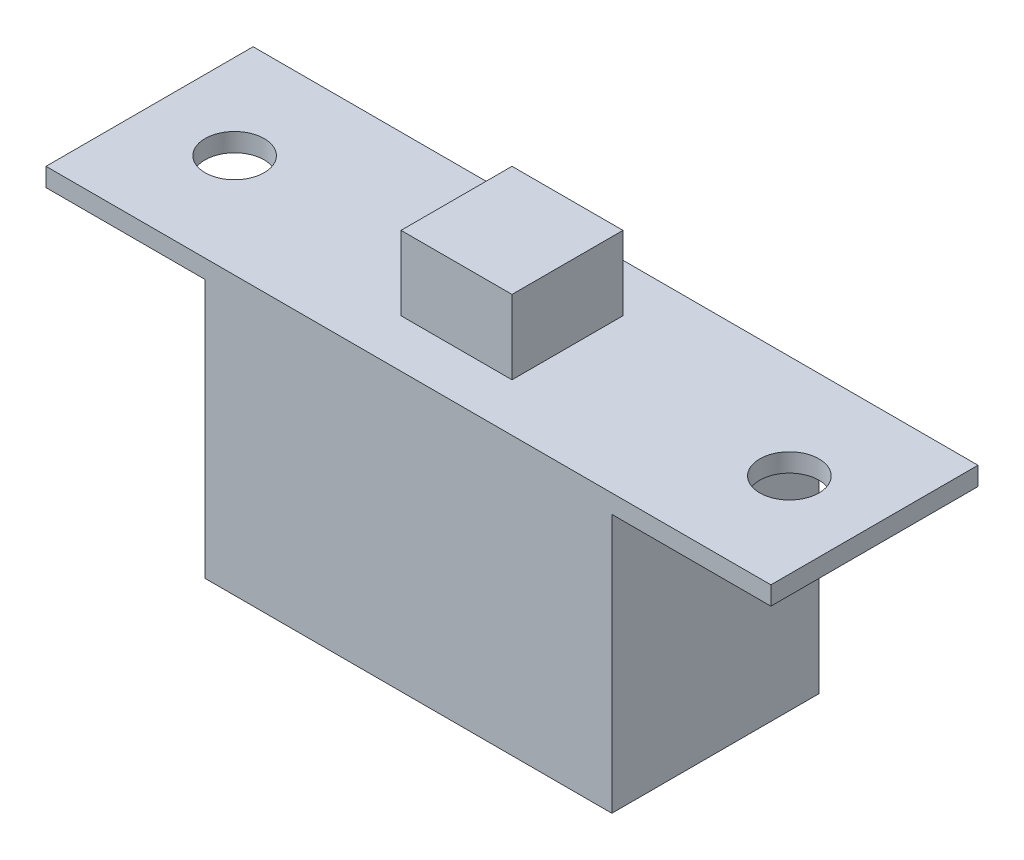
SolidWorks part; units mm, degrees
material "Unlegierter Baustahl"
ref_plane "Ebene vorne" through (0, 0, 0) normal (0, 0, 1) x (1, 0, 0)
ref_plane "Ebene oben" through (0, 0, 0) normal (0, 1, 0) x (1, 0, 0)
ref_plane "Ebene rechts" through (0, 0, 0) normal (1, 0, 0) x (0, 0, -1)
sketch "Skizze1" plane through (0, 0, 0) normal (0, 0, 1) x (1, 0, 0)
  line L0 (-9.8, -2) -> (-1.5, -2)
  line L1 (-1.5, -2) -> (-1.5, 0)
  line L2 (-1.5, 0) -> (1.5, 0)
  line L3 (0, 0) -> (0, -9.5) construction
  line L4 (-9.8, -2) -> (-9.8, -2.5)
  line L5 (-9.8, -2.5) -> (-5.5, -2.5)
  line L6 (-5.5, -2.5) -> (-5.5, -9.5)
  line L7 (-5.5, -9.5) -> (5.5, -9.5)
  line L8 (5.5, -2.5) -> (5.5, -9.5)
  line L9 (9.8, -2.5) -> (5.5, -2.5)
  line L10 (9.8, -2) -> (9.8, -2.5)
  line L11 (1.5, -2) -> (1.5, 0)
  line L12 (9.8, -2) -> (1.5, -2)
  dimension "D1" = 3
  dimension "D2" = 19.6
  dimension "D3" = 11
  dimension "D4" = 0.5
  dimension "D5" = 2
  dimension "D6" = 7
extrude "Aufsatz-Linear austragen1" add sketch "Skizze1" along normal mid plane 5.6
sketch "Skizze2" plane through (0, 0, 0) normal (0, 0, 1) x (1, 0, 0)
  line L1 (1.5, -2) -> (-1.5, -2)
  line L2 (1.5, -2) -> (1.5, 0)
  line L3 (1.5, 0) -> (-1.5, 0)
  line L4 (-1.5, -2) -> (-1.5, 0)
  line L5 (1.5, -2) -> (-1.5, 0) construction
  line L6 (1.5, 0) -> (-1.5, -2) construction
  point P0 (0, -1)
extrude "Schnitt-Linear austragen1" cut sketch "Skizze2" along normal through all from offset 1.5
mirror "Spiegeln1" about plane through (0, 0, 0) normal (0, 0, 1) of "Schnitt-Linear austragen1"
hole_wizard "M2 Gewindebohrung1" positions "Skizze3" profile "Skizze4" tap size "M2" standard "DIN" end condition through all
sketch "Skizze3" plane through (0, -2, 0) normal (0, 1, 0) x (1, 0, 0)
  point P0 (-7.5, 0)
  point P2 (7.5, 0)
  dimension "D1" = 7.5
  dimension "D2" = 7.5
sketch "Skizze4" plane through (-7.5, -2, 0) normal (1, 0, 0) x (0, 0, 1)
  line L0 (0, 0) -> (0, 7.5)
  line L1 (0, 7.5) -> (0.8, 7.5)
  line L2 (0.8, 7.5) -> (0.8, 0)
  line L5 (0.8, 0) -> (0, 0)
  line L11 (0, -6.35) -> (0, 107.95) construction
  dimension "Bohrerdurchmesser" = 1.6
  dimension "Bohrungstiefe" = 7.5
cosmetic thread "Bohrungsgewinde1" parameters "D2"=2
cosmetic thread "Bohrungsgewinde2" parameters "D2"=2
